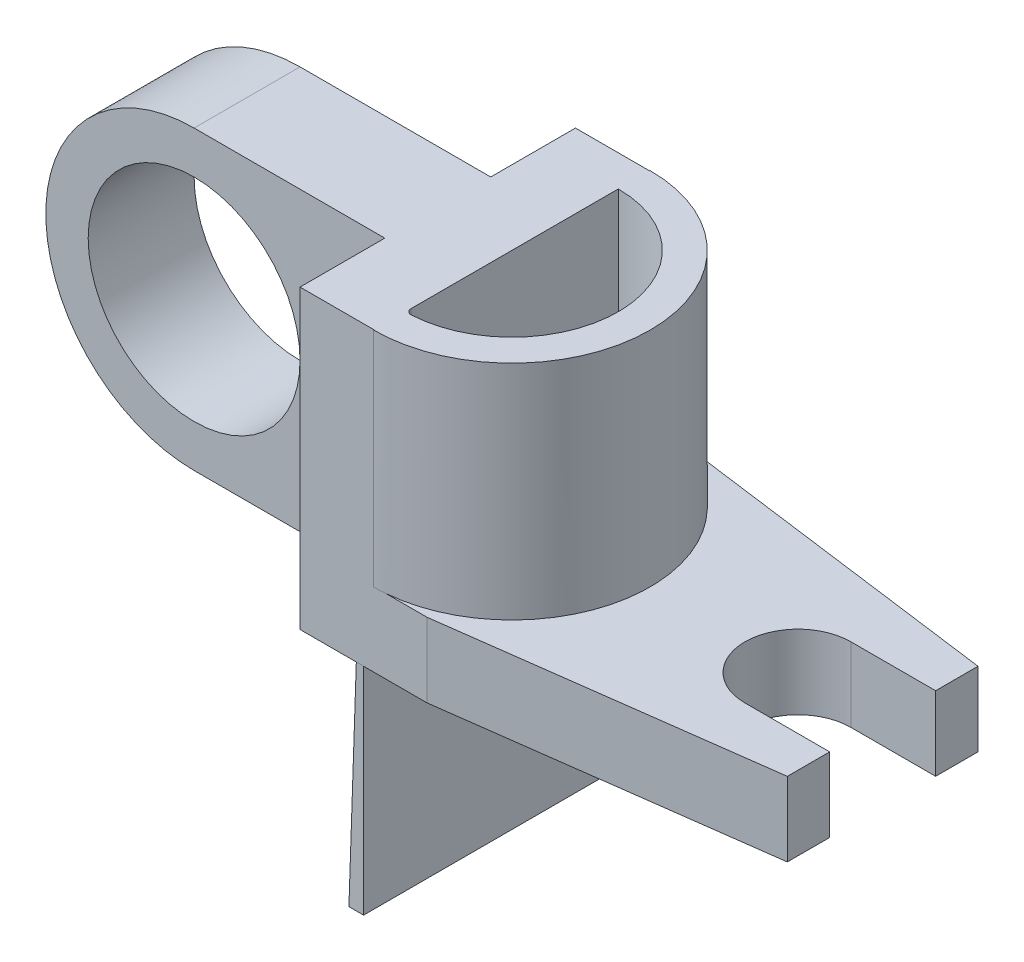
SolidWorks part; units mm, degrees
ref_plane "Płaszczyzna przednia" through (0, 0, 0) normal (0, 0, 1) x (1, 0, 0)
ref_plane "Płaszczyzna górna" through (0, 0, 0) normal (0, 1, 0) x (1, 0, 0)
ref_plane "Płaszczyzna prawa" through (0, 0, 0) normal (1, 0, 0) x (0, 0, -1)
sketch "Szkic1" plane through (0, 0, 0) normal (0, 0, 1) x (1, 0, 0)
  line L0 (-10.5939, 20.4485) -> (-10.5939, -7.5515)
  line L5 (-10.5939, 20.4485) -> (-28.5939, 20.4485)
  line L7 (-10.5939, -7.5515) -> (-28.5939, -7.5515)
  arc A1 (-28.5939, 20.4485) -> (-28.5939, -7.5515) centre (-28.5939, 6.4485) ccw
  circle A2 centre (-28.5939, 6.4485) radius 10
  dimension "D2" = 20
  dimension "D3" = 14
  dimension "D1" = 18
extrude "Dodanie-wyciągnięcie1" add sketch "Szkic1" along normal blind 10
sketch "Szkic2" plane through (-10.5939, 0, 0) normal (1, 0, 0) x (0, 0, -1)
  line L1 (-10, 20.4485) -> (-18, 20.4485)
  line L3 (-10, -7.5515) -> (-18, -7.5515)
  line L4 (-18, 20.4485) -> (-18, -7.5515)
  line L5 (0, -7.5515) -> (8, -7.5515)
  line L7 (0, 20.4485) -> (8, 20.4485)
  line L8 (8, -7.5515) -> (8, 20.4485)
  line L9 (-10, 20.4485) -> (0, 20.4485)
  line L11 (-10, -7.5515) -> (0, -7.5515)
  dimension "D1" = 8
  dimension "D2" = 8
extrude "Dodanie-wyciągnięcie2" add sketch "Szkic2" along normal blind 7 contours L1 L4 L3 L11 L5 L8 L7 L9
sketch "Szkic3" plane through (-3.5939, 0, 0) normal (1, 0, 0) x (0, 0, -1)
  line L0 (8, -7.5515) -> (8, 20.4485) construction
  line L1 (-18, -7.5515) -> (8, -7.5515)
  line L2 (-18, -7.5515) -> (-18, -0.5515)
  line L3 (-18, -0.5515) -> (8, -0.5515)
  line L4 (8, -7.5515) -> (8, -0.5515)
  dimension "D1" = 7
extrude "Dodanie-wyciągnięcie3" add sketch "Szkic3" along normal blind 5 contours L2 L1 L4 L3
sketch "Szkic4" plane through (0, -0.5515, 0) normal (0, 1, 0) x (1, 0, 0)
  line L2 (1.4061, -18) -> (1.4061, 8)
  line L4 (31.4061, -14) -> (31.4061, -10)
  line L8 (23.4061, -10) -> (31.4061, -10)
  line L9 (23.4061, 0) -> (31.4061, 0)
  line L10 (31.4061, 0) -> (31.4061, 4)
  line L11 (1.4061, 8) -> (31.4061, 4)
  line L12 (1.4061, -18) -> (31.4061, -14)
  arc A0 (23.4061, 0) -> (23.4061, -10) centre (23.4061, -5) ccw
  dimension "D2" = 8
  dimension "D5" = 5
  dimension "D1" = 4
  dimension "D3" = 4
  dimension "D4" = 18
  dimension "D6" = 30
extrude "Dodanie-wyciągnięcie4" add sketch "Szkic4" against normal blind 7 contours L4 L8 A0 L9 L10 L11 L2 L12
sketch "Szkic5" plane through (0, -0.5515, 0) normal (0, 1, 0) x (1, 0, 0)
  line L0 (-3.5939, -18) -> (-3.5939, 8) construction
  line L1 (-3.5939, 8.0439) -> (-3.5939, 5.0439)
  line L2 (-3.5939, -15.0439) -> (-3.5939, -18.0439)
  arc A0 (-3.5939, 5.0439) -> (-3.5939, -15.0439) centre (-3.5939, -5) cw
  arc A1 (-3.5939, 8.0439) -> (-3.5939, -18.0439) centre (-3.5939, -5) cw
  dimension "D1" = 3
extrude "Dodanie-wyciągnięcie5" add sketch "Szkic5" along normal up to surface (21 mm away) up to face at (-13.3439, 20.4485, 5)
sketch "Szkic6" plane through (0, 20.4485, 0) normal (0, 1, 0) x (1, 0, 0)
  line L0 (-10.5939, -10) -> (-28.5939, -10) construction
  line L1 (-30.5939, -10) -> (-15.5939, -10)
  line L2 (-30.5939, -10) -> (-30.5939, -18)
  line L3 (-30.5939, -18) -> (-15.5939, -18)
  line L4 (-15.5939, -10) -> (-15.5939, -18)
  line L5 (-10.5939, -10) -> (-10.5939, -18) construction
  dimension "D1" = 8
  dimension "D2" = 15
  dimension "D3" = 5
ref_plane "Płaszczyzna1" through (0, 0, 5) normal (0, 0, 1) x (1, 0, 0)
fillet "Zaokrąglenie2" radius 0.5 1 edges at (-3.5939, 9.9485, 15.0439)
sketch "Szkic8" plane through (0, -7.5515, 0) normal (0, -1, 0) x (1, 0, 0)
  line L0 (1.4061, 18) -> (-10.5939, 18) construction
  line L1 (-4.5939, 18) -> (-5.2819, 18)
  line L2 (-4.5939, 18) -> (-4.5939, -8)
  line L3 (-4.5939, -8) -> (-5.2819, -8)
  line L4 (-5.2819, 18) -> (-5.2819, -8)
  line L5 (1.4061, -8) -> (-10.5939, -8) construction
extrude "Dodanie-wyciągnięcie6" add sketch "Szkic8" along normal blind 20 draft 1 and the other way blind 10 draft outward yes
